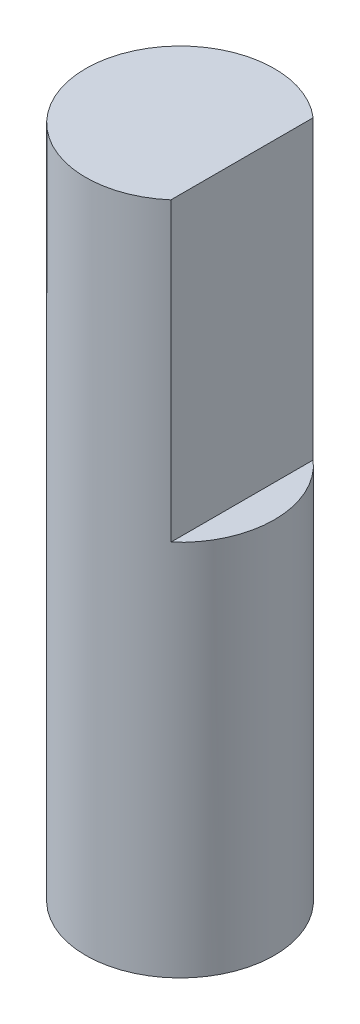
SolidWorks part; units mm, degrees
ref_plane "Front Plane" through (0, 0, 0) normal (0, 0, 1) x (1, 0, 0)
ref_plane "Top Plane" through (0, 0, 0) normal (0, 1, 0) x (1, 0, 0)
ref_plane "Right Plane" through (0, 0, 0) normal (1, 0, 0) x (0, 0, -1)
sketch "Sketch1" plane through (0, 0, 0) normal (0, 1, 0) x (1, 0, 0)
  circle A0 centre (0, 0) radius 3.5
  dimension "D1" = 7
extrude "Boss-Extrude1" add sketch "Sketch1" along normal blind 25
ref_plane "Plane1" through (0, 0, -3.5) normal (0, 0, -1) x (-1, 0, 0)
sketch "Sketch2" plane through (0, 0, -3.5) normal (0, 0, -1) x (-1, 0, 0)
  line L1 (-3.5, 25) -> (-2.3, 25)
  line L2 (-3.5, 25) -> (-3.5, 14)
  line L3 (-3.5, 14) -> (-2.3, 14)
  line L4 (-2.3, 25) -> (-2.3, 14)
  dimension "D1" = 11
  dimension "D2" = 1.2
extrude "Cut-Extrude1" cut sketch "Sketch2" against normal through all both and the other way through all
sketch "Sketch4" plane through (0, 25, 0) normal (0, 1, 0) x (1, 0, 0)
